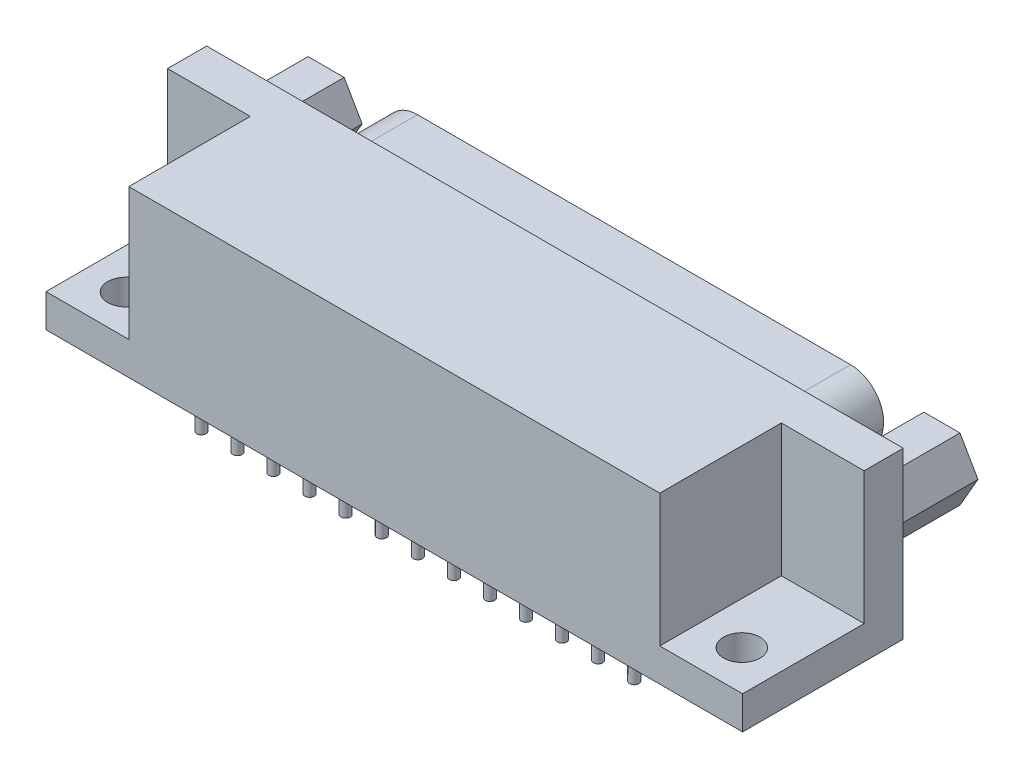
SolidWorks part; units mm, degrees
ref_plane "Front Plane" through (0, 0, 0) normal (0, 0, 1) x (1, 0, 0)
ref_plane "Top Plane" through (0, 0, 0) normal (0, 1, 0) x (1, 0, 0)
ref_plane "Right Plane" through (0, 0, 0) normal (1, 0, 0) x (0, 0, -1)
sketch "Sketch1" plane through (0, 0, 0) normal (0, 1, 0) x (1, 0, 0)
  line L1 (-10.16, -1.77) -> (43.31, -1.77)
  line L2 (-10.16, -1.77) -> (-10.16, 10.56)
  line L3 (-10.16, 10.56) -> (43.31, 10.56)
  line L4 (43.31, -1.77) -> (43.31, 10.56)
  point P3 (16.575, 10.56)
  dimension "D1" = 53.47
  dimension "D2" = 12.33
  dimension "D3" = 1.77
  dimension "D4" = 10.16
extrude "Base-Extrude" add sketch "Sketch1" along normal blind 12.7
sketch "Sketch2" plane through (0, 0, -10.56) normal (0, 0, -1) x (-1, 0, 0)
  line L0 (-16.575, 12.7) -> (-16.575, -6.5379) construction
  line L1 (-43.31, 12.7) -> (10.16, 12.7) construction
  line L2 (-32.6544, 2.286) -> (-0.4956, 2.286)
  line L3 (1.9982, 4.3435) -> (2.5388, 7.1375)
  line L4 (0.045, 10.16) -> (-33.195, 10.16)
  line L6 (-35.1482, 4.3435) -> (-35.6888, 7.1375)
  line L7 (-43.31, 0) -> (10.16, 0) construction
  arc A0 (1.9982, 4.3435) -> (-0.4956, 2.286) centre (-0.4956, 4.826) cw
  arc A1 (0.045, 10.16) -> (2.5388, 7.1375) centre (0.045, 7.62) cw
  arc A2 (-33.195, 10.16) -> (-35.6888, 7.1375) centre (-33.195, 7.62) ccw
  arc A3 (-35.1482, 4.3435) -> (-32.6544, 2.286) centre (-32.6544, 4.826) ccw
  point P4 (-16.575, 10.16)
  point P12 (1.6001, 2.286)
  point P21 (-16.575, 2.286)
  dimension "D5" = 2.54
  dimension "D1" = 2.286
  dimension "D2" = 2.54
  dimension "D3" = 100.95
  dimension "D4" = 33.24
extrude "Boss-Extrude1" add sketch "Sketch2" along normal blind 6.07
sketch "Sketch4" plane through (0, 0, -16.63) normal (0, 0, -1) x (-1, 0, 0)
  line L0 (10.16, 12.7) -> (10.16, 0) construction
  line L2 (-43.31, 12.7) -> (10.16, 12.7) construction
  circle A0 centre (0, 7.62) radius 0.5
  dimension "D1" = 1
  dimension "D2" = 10.16
  dimension "D3" = 5.08
extrude "Cut-Extrude1" cut sketch "Sketch4" against normal blind 5.08
sketch "Sketch5" plane through (0, 0, -16.63) normal (0, 0, -1) x (-1, 0, 0)
  line L0 (10.16, 12.7) -> (10.16, 0) construction
  line L2 (-43.31, 0) -> (10.16, 0) construction
  circle A0 centre (-1.397, 5.08) radius 0.5
  circle A1 centre (0, 7.62) radius 0.5 construction
  dimension "D2" = 5.08
  dimension "D1" = 11.557
extrude "Cut-Extrude2" cut sketch "Sketch5" against normal blind 5.08
sketch "Sketch6" plane through (0, 0, 0) normal (0, -1, 0) x (1, 0, 0)
  circle A0 centre (0, 0) radius 0.3556
  dimension "D1" = 0.7112
extrude "Boss-Extrude2" add sketch "Sketch6" along normal blind 2.54
pattern_linear "LPattern1" count 13 spacing 2.7686 along (1, 0, 0) of "Boss-Extrude2"
pattern_linear "LPattern2" count 13 spacing 2.7686 along (1, 0, 0) of "Cut-Extrude1"
pattern_linear "LPattern3" count 12 spacing 2.7686 along (1, 0, 0) of "Cut-Extrude2"
sketch "Sketch7" plane through (0, 0, 0) normal (0, -1, 0) x (1, 0, 0)
  line L1 (-10.16, -10.56) -> (-10.16, 1.77) construction
  circle A0 centre (1.397, -2.54) radius 0.3556
  dimension "D1" = 0.7112
  dimension "D2" = 11.557
  dimension "D3" = 2.54
extrude "Boss-Extrude3" add sketch "Sketch7" along normal up to surface (2.54 mm away) up to face at (0, -2.54, -0.3556)
pattern_linear "LPattern4" count 12 spacing 2.7686 along (1, 0, 0) of "Boss-Extrude3"
ref_plane "Centreline Plane" through (16.575, 0, 0) normal (1, 0, 0) x (0, 0, -1)
sketch "Sketch12" plane through (0, 0, -10.56) normal (0, 0, -1) x (-1, 0, 0)
  line L0 (-43.31, 12.7) -> (10.16, 12.7) construction
  line L1 (-41.595, 9.82) -> (-42.98, 7.4211)
  line L2 (-42.98, 7.4211) -> (-41.595, 5.0222)
  line L3 (-41.595, 5.0222) -> (-38.825, 5.0222)
  line L4 (-38.825, 5.0222) -> (-37.44, 7.4211)
  line L5 (-37.44, 7.4211) -> (-38.825, 9.82)
  line L6 (-38.825, 9.82) -> (-41.595, 9.82)
  line L7 (-43.31, 12.7) -> (-43.31, 0) construction
  circle A0 centre (-40.21, 7.4211) radius 2.3989 construction
  circle A1 centre (-40.21, 7.4211) radius 1.3043
  dimension "D1" = 2.77
  dimension "D2" = 2.88
  dimension "D3" = 0.33
extrude "Boss-Extrude4" add sketch "Sketch12" along normal blind 6.07
sketch "Sketch9" plane through (0, 0, 1.77) normal (0, 0, 1) x (1, 0, 0)
  line L1 (-10.16, 12.7) -> (-3.8049, 12.7)
  line L2 (-10.16, 12.7) -> (-10.16, 2.54)
  line L3 (-10.16, 2.54) -> (-3.8049, 2.54)
  line L4 (-3.8049, 12.7) -> (-3.8049, 2.54)
  dimension "D1" = 10.16
  dimension "D2" = 6.3551
extrude "Cut-Extrude3" cut sketch "Sketch9" against normal blind 9.33
sketch "Sketch11" plane through (0, 2.54, 0) normal (0, 1, 0) x (-1, 0, 0)
  line L0 (10.16, 1.77) -> (3.8049, 1.77) construction
  line L1 (10.16, -7.56) -> (10.16, 1.77) construction
  circle A0 centre (7.06, -1.27) radius 1.4
  point P2 (6.9825, 1.77)
  dimension "D1" = 2.8
  dimension "D2" = 3.04
  dimension "D3" = 3.1
extrude "Cut-Extrude4" cut sketch "Sketch11" against normal through all
mirror "Mirror1" about plane through (16.575, 0, 0) normal (1, 0, 0) of "Boss-Extrude4", "Cut-Extrude3", "Cut-Extrude4"
sketch "Component_Outline" plane through (0, 0, 0) normal (0, -1, 0) x (1, 0, 0)
  line L0 (32.6544, -16.63) -> (0.4956, -16.63) construction
  line L1 (-10.16, 1.77) -> (43.31, 1.77)
  line L2 (-10.16, 1.77) -> (-10.16, -16.63)
  line L3 (-10.16, -16.63) -> (43.31, -16.63)
  line L4 (43.31, 1.77) -> (43.31, -16.63)
  line L5 (43.31, 1.77) -> (43.31, -10.56) construction
